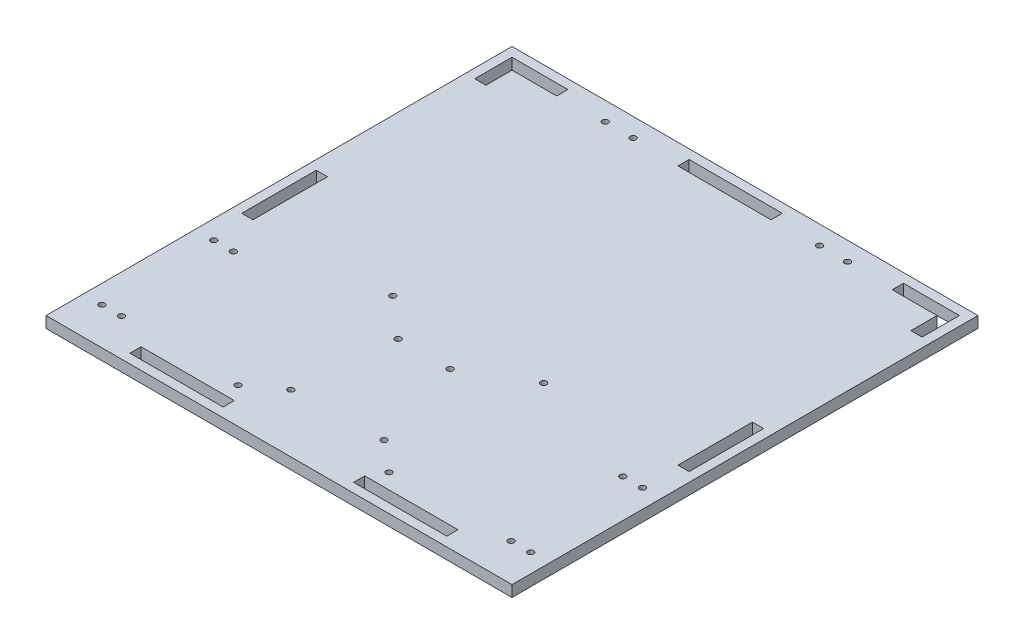
SolidWorks part; units mm, degrees
ref_plane "Front Plane" through (0, 0, 0) normal (0, 0, 1) x (1, 0, 0)
ref_plane "Top Plane" through (0, 0, 0) normal (0, 1, 0) x (1, 0, 0)
ref_plane "Right Plane" through (0, 0, 0) normal (1, 0, 0) x (0, 0, -1)
sketch "Sketch1" plane through (0, 0, 0) normal (0, 1, 0) x (1, 0, 0)
  line L1 (125, 125) -> (-125, 125)
  line L2 (125, 125) -> (125, -125)
  line L3 (125, -125) -> (-125, -125)
  line L4 (-125, 125) -> (-125, -125)
  line L5 (125, 125) -> (-125, -125) construction
  line L6 (125, -125) -> (-125, 125) construction
  point P0 (0, 0)
  dimension "D1" = 250
  dimension "D2" = 250
extrude "Boss-Extrude1" add sketch "Sketch1" along normal blind 6
sketch "Sketch4" plane through (0, 6, 0) normal (0, 1, 0) x (1, 0, 0)
  line L0 (-125, -125) -> (125, -125) construction
  line L1 (-125, 125) -> (-125, -125) construction
  line L2 (0, 141.9283) -> (0, -157.9709) construction
  line L3 (-206.4723, 0) -> (192.8578, 0) construction
  circle A0 centre (-115, -105) radius 1.6
  circle A1 centre (-104.5, -105) radius 1.6
  circle A2 centre (-115, -45) radius 1.6
  circle A3 centre (-104.5, -45) radius 1.6
  circle A4 centre (115, -45) radius 1.6
  circle A5 centre (104.5, -45) radius 1.6
  circle A6 centre (115, -105) radius 1.6
  circle A7 centre (104.5, -105) radius 1.6
  dimension "D1" = 3.2
  dimension "D2" = 60
  dimension "D3" = 10.5
  dimension "D4" = 20
  dimension "D5" = 10
extrude "Cut-Extrude2" cut sketch "Sketch4" against normal up to next
sketch "Sketch5" plane through (0, 6, 0) normal (0, 1, 0) x (1, 0, 0)
  line L0 (0, 0) -> (0, 169.9644) construction
  line L1 (-125, 125) -> (-125, -125) construction
  line L2 (125, 125) -> (-125, 125) construction
  circle A0 centre (-65, 115) radius 1.6
  circle A1 centre (-50, 115) radius 1.6
  circle A2 centre (50, 115) radius 1.6
  circle A3 centre (65, 115) radius 1.6
  dimension "D1" = 3.2
  dimension "D2" = 15
  dimension "D3" = 60
  dimension "D4" = 10
extrude "Cut-Extrude3" cut sketch "Sketch5" against normal up to next
sketch "Sketch6" plane through (0, 6, 0) normal (0, 1, 0) x (1, 0, 0)
  line L1 (-120, 120) -> (-112.4662, 120)
  line L2 (-120, 120) -> (-120, 100)
  line L3 (-120, 100) -> (-114, 100)
  line L4 (-114, 114) -> (-114, 100)
  line L5 (-120, 15) -> (-114, 15)
  line L6 (-120, 15) -> (-120, -25)
  line L7 (-120, -25) -> (-114, -25)
  line L8 (-114, 15) -> (-114, -25)
  line L9 (-125, -125) -> (125, -125) construction
  line L10 (-85, -120) -> (-35, -120)
  line L11 (-85, -120) -> (-85, -114)
  line L12 (-85, -114) -> (-35, -114)
  line L13 (-35, -120) -> (-35, -114)
  line L15 (35, -120) -> (85, -120)
  line L16 (35, -120) -> (35, -114)
  line L17 (35, -114) -> (85, -114)
  line L18 (85, -120) -> (85, -114)
  line L19 (120, 120) -> (114.723, 120)
  line L20 (120, 120) -> (120, 100)
  line L21 (120, 100) -> (114, 100)
  line L22 (114, 114) -> (114, 100)
  line L23 (120, 15) -> (114, 15)
  line L24 (120, 15) -> (120, -25)
  line L25 (120, -25) -> (114, -25)
  line L26 (114, 15) -> (114, -25)
  line L27 (125, 125) -> (-125, 125) construction
  line L28 (-25, 120) -> (25, 120)
  line L29 (-25, 120) -> (-25, 114)
  line L30 (-25, 114) -> (25, 114)
  line L31 (25, 120) -> (25, 114)
  line L32 (-125, 125) -> (-125, -125) construction
  line L33 (-120, 120) -> (-90, 120)
  line L34 (-120, 120) -> (-120, 118.2194)
  line L35 (-114, 114) -> (-90, 114)
  line L36 (-90, 120) -> (-90, 114)
  line L37 (120, 120) -> (90, 120)
  line L38 (120, 120) -> (120, 118.2194)
  line L39 (114, 114) -> (90, 114)
  line L40 (90, 120) -> (90, 114)
  line L41 (125, -125) -> (125, 125) construction
  point P48 (0, 120)
  point P49 (0, 125)
  dimension "D1" = 6
  dimension "D2" = 6
  dimension "D3" = 6
  dimension "D4" = 6
  dimension "D5" = 6
  dimension "D6" = 6
  dimension "D7" = 6
  dimension "D8" = 6
  dimension "D9" = 6
  dimension "D12" = 50
  dimension "D13" = 50
  dimension "D14" = 100
  dimension "D15" = 40
  dimension "D16" = 20
  dimension "D17" = 30
  dimension "D18" = 30
  dimension "D19" = 50
  dimension "D10" = 40
  dimension "D11" = 40
  dimension "D20" = 5
  dimension "D21" = 5
  dimension "D22" = 5
  dimension "D23" = 5
extrude "Cut-Extrude6" cut sketch "Sketch6" against normal up to surface (6 mm away)
sketch "Sketch7" plane through (0, 0, 0) normal (0, -1, 0) x (-1, 0, 0)
  circle A0 centre (19.693, -41.4) radius 1.6
  circle A1 centre (-8.207, -41.4) radius 1.6
  circle A2 centre (-23.507, -92.2) radius 1.6
  circle A3 centre (24.793, -93.8) radius 1.6
  dimension "D1" = 3.2
  dimension "D2" = 3.2
  dimension "D3" = 3.2
  dimension "D4" = 3.2
extrude "Cut-Extrude7" cut sketch "Sketch7" against normal up to next
sketch "Sketch8" plane through (0, 0, 0) normal (0, -1, 0) x (-1, 0, 0)
  circle A0 centre (41.143, -105.8383) radius 1.6
  circle A1 centre (41.143, -22.8383) radius 1.6
  circle A2 centre (-39.857, -22.8383) radius 1.6
  circle A3 centre (-39.857, -105.8383) radius 1.6
  dimension "D1" = 3.2
  dimension "D2" = 3.2
  dimension "D3" = 3.2
  dimension "D4" = 3.2
extrude "Cut-Extrude8" cut sketch "Sketch8" against normal up to next
equation "\"Material Thickness\"= 6"
equation "\"D1@Sketch6\"=\"Material Thickness\""
equation "\"D2@Sketch6\"=\"Material Thickness\""
equation "\"D4@Sketch6\"=\"Material Thickness\""
equation "\"D5@Sketch6\"=\"Material Thickness\""
equation "\"D6@Sketch6\"=\"Material Thickness\""
equation "\"D7@Sketch6\"=\"Material Thickness\""
equation "\"D8@Sketch6\"=\"Material Thickness\""
equation "\"D9@Sketch6\"=\"Material Thickness\""
equation "\"D12@Sketch6\"=\"D13@Sketch6\""
equation "\"D18@Sketch6\"=\"D17@Sketch6\""
equation "\"D3@Sketch6\"=\"Material Thickness\""
equation "\"D1@Boss-Extrude1\"=\"Material Thickness\""
equation "\"D10@Sketch6\"=\"D11@Sketch6\""
